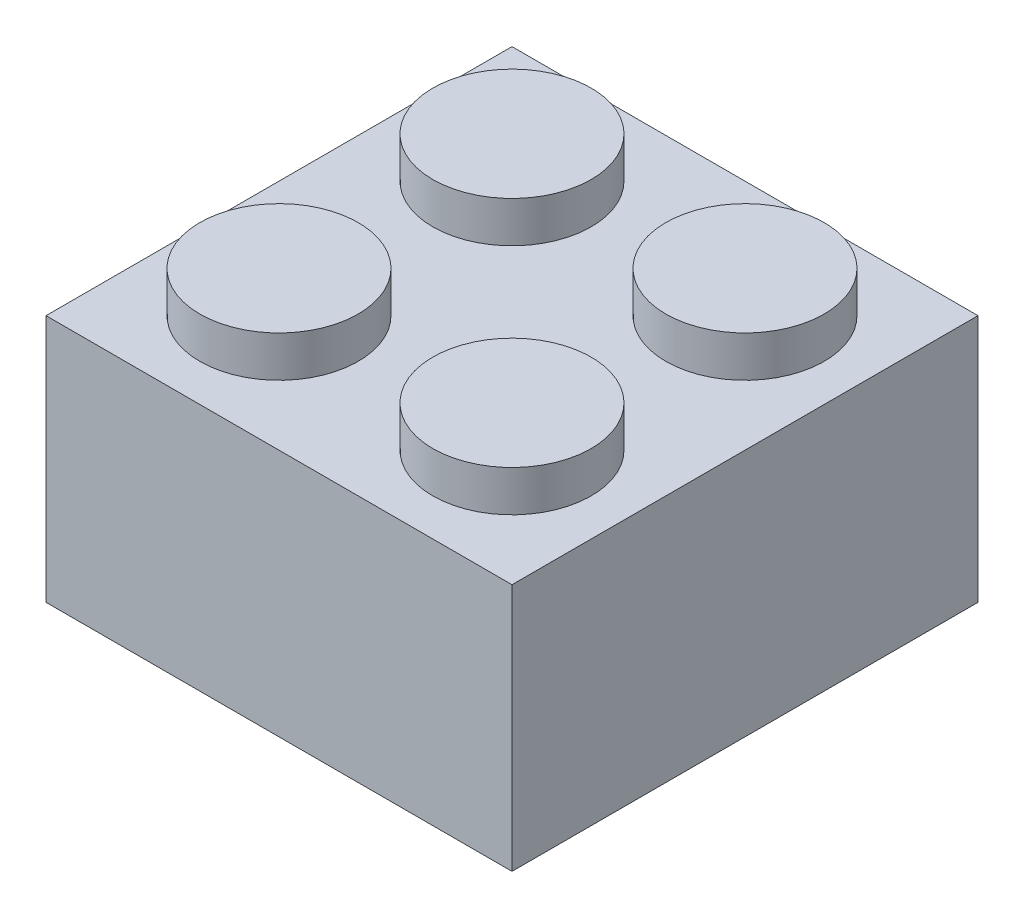
SolidWorks part; units mm, degrees
material "ABS"
ref_plane "Front Plane" through (0, 0, 0) normal (0, 0, 1) x (1, 0, 0)
ref_plane "Top Plane" through (0, 0, 0) normal (0, 1, 0) x (1, 0, 0)
ref_plane "Right Plane" through (0, 0, 0) normal (1, 0, 0) x (0, 0, -1)
sketch "Sketch1" plane through (0, 0, 0) normal (0, 1, 0) x (1, 0, 0)
  line L1 (-7.9375, 7.9375) -> (7.9375, 7.9375)
  line L2 (-7.9375, 7.9375) -> (-7.9375, -7.9375)
  line L3 (-7.9375, -7.9375) -> (7.9375, -7.9375)
  line L4 (7.9375, 7.9375) -> (7.9375, -7.9375)
  line L5 (-7.9375, 7.9375) -> (7.9375, -7.9375) construction
  line L6 (-7.9375, -7.9375) -> (7.9375, 7.9375) construction
  point P0 (0, 0)
  dimension "D1" = 15.875
extrude "Boss-Extrude1" add sketch "Sketch1" along normal mid plane 8.4582
sketch "Sketch2" plane through (0, -4.2291, 0) normal (0, -1, 0) x (1, 0, 0)
  line L12 (6.6675, -6.6675) -> (6.6675, 6.6675)
  line L13 (6.6675, 6.6675) -> (-6.6675, 6.6675)
  line L14 (-6.6675, 6.6675) -> (-6.6675, -6.6675)
  line L15 (-6.6675, -6.6675) -> (6.6675, -6.6675)
  line L16 (6.6675, -6.6675) -> (6.6675, 6.6675)
  line L17 (6.6675, 6.6675) -> (-6.6675, 6.6675)
  line L18 (-6.6675, 6.6675) -> (-6.6675, -6.6675)
  line L19 (-6.6675, -6.6675) -> (6.6675, -6.6675)
  circle A0 centre (0, 0) radius 3.175
  circle A1 centre (0, 0) radius 2.413
  dimension "D2" = 6.35
  dimension "D3" = 0.762
  dimension "D1" = 1.27
extrude "Cut-Extrude1" cut sketch "Sketch2" against normal offset from surface (7.1882 mm away) 1.27 contours L18 L19 L16 L17 A0 | A1 up to face at (0, 4.2291, 0)
sketch "Sketch3" plane through (0, 4.2291, 0) normal (0, 1, 0) x (1, 0, 0)
  line L0 (7.9375, -7.9375) -> (7.9375, 7.9375) construction
  line L1 (-7.9375, -7.9375) -> (7.9375, -7.9375) construction
  circle A0 centre (3.9688, -3.9688) radius 2.6987
  dimension "D3" = 5.3975
  dimension "D1" = 3.9688
  dimension "D2" = 3.9688
extrude "Boss-Extrude2" add sketch "Sketch3" along normal blind 1.397
pattern_linear "LPattern1" count 2 spacing 7.9375 along (-1, 0, 0) count 2 spacing 7.9375 along (0, 0, -1) of "Boss-Extrude2"
